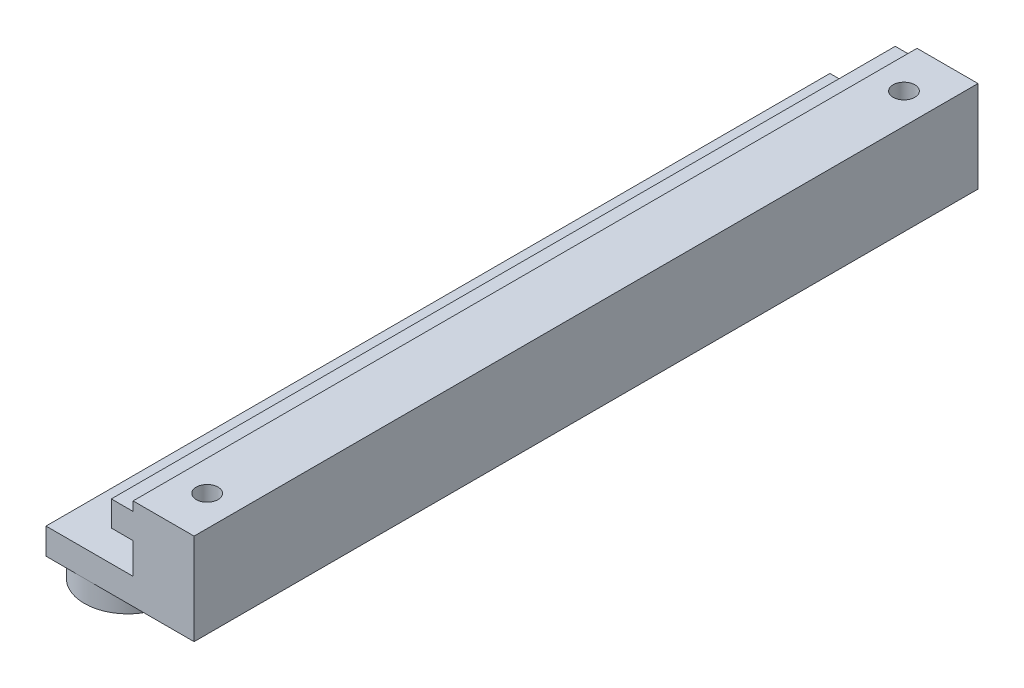
SolidWorks part; units mm, degrees
ref_plane "Front Plane" through (0, 0, 0) normal (0, 0, 1) x (1, 0, 0)
ref_plane "Top Plane" through (0, 0, 0) normal (0, 1, 0) x (1, 0, 0)
ref_plane "Right Plane" through (0, 0, 0) normal (1, 0, 0) x (0, 0, -1)
sketch "Sketch1" plane through (0, 0, 0) normal (0, 0, 1) x (1, 0, 0)
  line L0 (-10, 7.5) -> (0, 7.5)
  line L1 (0, 7.5) -> (0, 3.95)
  line L2 (0, 3.95) -> (-2.5, 3.95)
  line L3 (-2.5, 3.95) -> (-2.5, 1.05)
  line L4 (-2.5, 1.05) -> (0, 1.05)
  line L5 (0, 1.05) -> (0, 0)
  line L6 (0, 0) -> (7, 0)
  line L7 (7, 0) -> (7, 10.5)
  line L8 (7, 10.5) -> (-10, 10.5)
  line L9 (-10, 10.5) -> (-10, 7.5)
  dimension "D1" = 3.55
  dimension "D2" = 2.5
  dimension "D3" = 3
  dimension "D4" = 7
  dimension "D5" = 10
  dimension "D6" = 2.9
  dimension "D7" = 1.05
extrude "Main" add sketch "Sketch1" along normal blind 90
sketch "Sketch2" plane through (0, 10.5, 0) normal (0, 1, 0) x (1, 0, 0)
  line L0 (7, -90) -> (-10, -90) construction
  line L1 (7, 0) -> (-10, 0) construction
  circle A0 centre (-5.6, -85) radius 5
  circle A1 centre (-5.6, -10.2) radius 5
  dimension "D1" = 10
  dimension "D2" = 74.8
  dimension "D3" = 5
  dimension "D4" = 5.6
  dimension "D5" = 10.2
extrude "Plot" add sketch "Sketch2" along normal blind 2.5
sketch "Sketch3" plane through (0, 13, 0) normal (0, 1, 0) x (1, 0, 0)
  circle A0 centre (-5.6, -10.2) radius 1.25
  circle A1 centre (-5.6, -85) radius 1.25
  dimension "D1" = 2.5
extrude "HoleFix" cut sketch "Sketch3" against normal through all
sketch "Sketch4" plane through (7, 0, 0) normal (0, 1, 0) x (0, 0, -1)
  line L0 (-90, 0) -> (0, 0) construction
  line L3 (0, 0) -> (0, 17) construction
  line L4 (-90, 0) -> (-90, 12.6) construction
  circle A0 centre (-85, 3.5) radius 1.25
  circle A1 centre (-5, 3.5) radius 1.25
  dimension "D1" = 2.5
  dimension "D2" = 3.5
  dimension "D3" = 5
  dimension "D4" = 5
  dimension "D5" = 80
extrude "Cut-Extrude4" cut sketch "Sketch4" along normal through all
ref_plane "Plane1" through (0, 18.5, 0) normal (0, 1, 0) x (1, 0, 0)
mirror "Mirror2" about plane through (0, 18.5, 0) normal (0, 1, 0)
sketch "Sketch5" plane through (0, 0, 90) normal (0, 0, 1) x (1, 0, 0)
  line L1 (12.768, 16.1276) -> (-18.7504, 16.1276)
  line L2 (12.768, 16.1276) -> (12.768, -3.0545)
  line L3 (12.768, -3.0545) -> (-18.7504, -3.0545)
  line L4 (-18.7504, 16.1276) -> (-18.7504, -3.0545)
extrude "Cut-Extrude5" cut sketch "Sketch5" against normal through all
